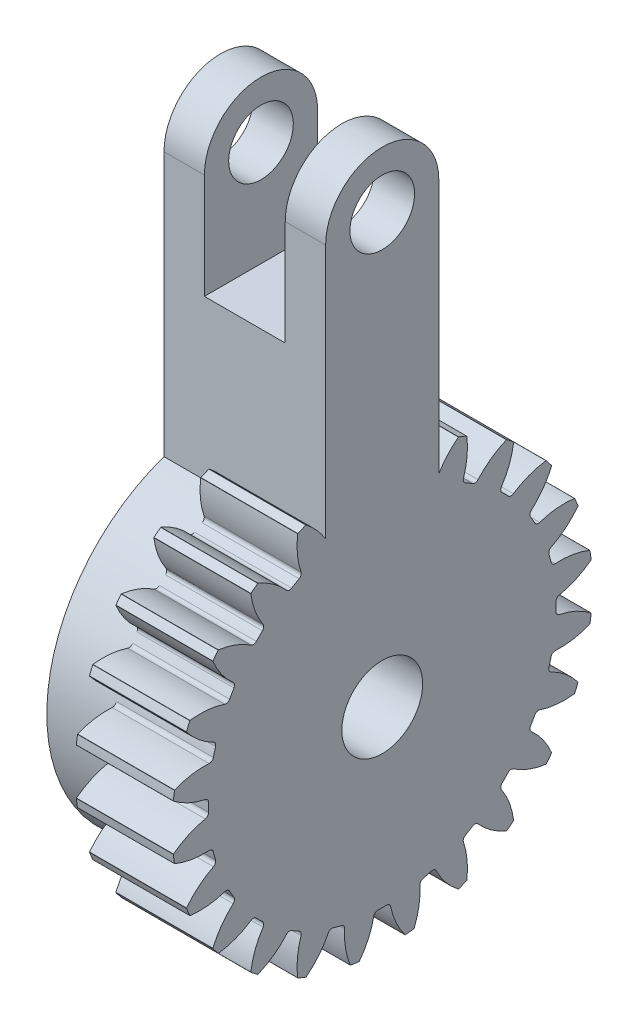
SolidWorks part; units mm, degrees
material "Nylon 101"
ref_plane "Plane1" through (0, 0, 0) normal (0, 0, 1) x (1, 0, 0)
ref_plane "Plane2" through (0, 0, 0) normal (0, 1, 0) x (1, 0, 0)
ref_plane "Plane3" through (0, 0, 0) normal (1, 0, 0) x (0, 0, -1)
sketch "HoldingSke" plane through (0, 0, 0) normal (0, 1, 0) x (1, 0, 0)
  line L0 (0, 0) -> (0.9135, -0.4067)
  line L1 (-15, 0) -> (100, 0) construction
  line L2 (0, 0) -> (-2.1039, 2.3779)
  line L3 (0, 0) -> (-11.863, 4.5341)
  line L4 (0, 0) -> (7.8894, 3.5126)
  line L5 (0, 0) -> (-46.8476, -17.4728)
  line L6 (0, 0) -> (-4.9738, -3.3558)
  line L7 (-2.1039, 2.3779) -> (8.6589, 51.2073)
  line L8 (-76.2, 54.61) -> (-75.5, 54.61)
  line L9 (-71.009, 38.7566) -> (-53.1078, 45.2721)
  line L10 (-76.2, 71.12) -> (104.1128, 71.12)
  line L11 (0, 0) -> (-6, 0)
  line L12 (-76.2, 101.6) -> (-76.162, 101.6)
  line L13 (24.9733, 27.94) -> (52.9518, 28.4284)
  line L14 (24.9733, 27.94) -> (24.9743, 27.94)
  line L15 (24.9733, 27.94) -> (100.4006, 29.5858)
  line L16 (-63.627, -1) -> (-12.827, -1)
  circle A0 centre (0, 0) radius 2
  circle A1 centre (0, 0) radius 10.749
  circle A2 centre (0, 0) radius 37.5
  circle A3 centre (0, 0) radius 2
  dimension "MHD" = 21.498
  dimension "Hub_dia" = 75
  dimension "Bore" = 4
  dimension "MBD" = 4
  dimension "Num_teeth" = 24
  dimension "Pitch" = 1
  dimension "Overall_len" = 50
  dimension "Show_teeth" = 24
  dimension "Thickness" = 6
  dimension "OAL" = 50.0015
  dimension "T_dim" = 0.7
  dimension "Ap" = 20
  dimension "H" = 19.05
  dimension "Pitch_radius" = 180.3128
  dimension "Width" = 6
  dimension "Backlash" = 0.038
  dimension "Addendum_fac" = 1
  dimension "Dedendum_fac" = 1.25
  dimension "Clearance_fac" = 0.25
  dimension "Dedendum_add" = 0.001
  dimension "Module" = 1
sketch "BasProSke" plane through (0, 0, 0) normal (0, 1, 0) x (1, 0, 0)
  line L0 (-10, 0) -> (60, 0) construction
  line L1 (0, 0) -> (0, 13)
  line L2 (0, 0) -> (6, 0)
  line L3 (6, 0) -> (6, 13)
  line L4 (6, 13) -> (0, 13)
  dimension "Thickness" = 6
  dimension "Diameter" = 26
revolve "Base-Revolve" add sketch "BasProSke" angle 360 about L0
sketch "TooCutSke" plane through (0, 0, 0) normal (1, 0, 0) x (0, 0, -1)
  line L1 (0, 0) -> (0, 107) construction
  line L2 (0, 0) -> (-0.8513, 11.9698) construction
  line L3 (0, 0) -> (-3.127, 23.752) construction
  line L4 (-0.8513, 11.9698) -> (-1.5635, 11.876) construction
  arc A0 (0.4834, 10.7381) -> (-0.4834, 10.7381) centre (0, 0) ccw
  arc A1 (1.4409, 12.9455) -> (-1.4409, 12.9455) centre (0, 0) ccw
  circle A2 centre (0, 0) radius 12 construction
  circle A3 centre (0, 0) radius 11.2763 construction
  arc A4 (-0.4834, 10.7381) -> (-1.4409, 12.9455) centre (-5.2252, 9.9926) ccw
  arc A5 (1.4409, 12.9455) -> (0.4834, 10.7381) centre (5.2252, 9.9926) ccw
  dimension "Root_dia" = 21.498
  dimension "Overcut_dia" = 26.0508
  dimension "Pitch_dia" = 24
  dimension "Base_dia" = 22.5526
  dimension "Flank_rad" = 4.8
  dimension "Half_ang" = 7.5
  dimension "Half_CT" = 0.7183
extrude "ToothCut" cut sketch "TooCutSke" along normal through all
fillet "Breaks" radius 0.02 2 edges at (3, 12.9219, -1.4227) (3, 12.9219, 1.4227)
fillet "RootFillets" radius 0.251 2 edges at (3, 10.7381, -0.4834) (3, 10.7381, 0.4834)
pattern_circular "TeethCuts" count 24 over 360 about axis through (0, 0, 0) along (1, 0, 0) of "ToothCut", "RootFillets", "Breaks"
sketch "HubNeaOneSke" plane through (0, 0, 0) normal (-1, 0, 0) x (0, 0, 1)
  circle A0 centre (0, 0) radius 10.749
  dimension "Diameter" = 21.498
extrude "HubNearOne" add sketch "HubNeaOneSke" along normal blind 4
sketch "HubNeaBotSke" plane through (0, 0, 0) normal (-1, 0, 0) x (0, 0, 1)
  circle A0 centre (0, 0) radius 10.749
  dimension "Diameter" = 21.498
extrude "HubNearBoth" add sketch "HubNeaBotSke" along normal blind 4
sketch "BorSke" plane through (0, 0, 0) normal (1, 0, 0) x (0, 0, -1)
  circle A0 centre (0, 0) radius 2.5
  dimension "Diameter" = 5
extrude "Bore" cut sketch "BorSke" along normal mid plane 100.003
ref_plane "FarPln" through (6, 0, 0) normal (1, 0, 0) x (0, 0, -1)
sketch "HubFarSke" plane through (6, 0, 0) normal (1, 0, 0) x (0, 0, -1)
  circle A0 centre (0, 0) radius 10.749
  dimension "Diameter" = 21.498
extrude "HubFar" [suppressed] add sketch "HubFarSke" along normal blind 22.0008
sketch "Эскиз1" plane through (0, 0, 0) normal (-1, 0, 0) x (0, 0, 1)
  circle A0 centre (0, 0) radius 9
  dimension "D1" = 18
extrude "Бобышка-Вытянуть1" add sketch "Эскиз1" along normal blind 4
sketch "Эскиз2" plane through (-4, 0, 0) normal (-1, 0, 0) x (0, 0, 1)
  circle A0 centre (0, 0) radius 2.5
  dimension "D1" = 5
extrude "Вырез-Вытянуть1" cut sketch "Эскиз2" against normal through all
sketch "Эскиз3" plane through (0, 0, 0) normal (1, 0, 0) x (0, 0, -1)
  line L0 (0, 0) -> (0, 30) construction
  line L1 (-3.5, 26.5) -> (-3.5, 7)
  line L2 (3.5, 26.5) -> (3.5, 7)
  line L4 (3.5, 7) -> (-3.5, 7)
  arc A0 (-3.5, 26.5) -> (3.5, 26.5) centre (0, 26.5) cw
  dimension "D4" = 7
  dimension "D3" = 3.5
  dimension "D1" = 30
  dimension "D2" = 26.5
extrude "Бобышка-Вытянуть2" add sketch "Эскиз3" along normal blind 6 and the other way blind 4
sketch "Эскиз4" plane through (0, 0, 0) normal (0, 0, 1) x (1, 0, 0)
  line L0 (-1.5, 32) -> (3.5, 32)
  line L1 (-1.5, 32) -> (-1.5, 20)
  line L2 (-1.5, 20) -> (3.5, 20)
  line L3 (3.5, 32) -> (3.5, 20)
  line L4 (0, 10.749) -> (0, -10.749) construction
  line L5 (-4, 30) -> (-4, 26.5) construction
  point P6 (0, 0)
  dimension "D1" = 12
  dimension "D2" = 5
  dimension "D3" = 20
  dimension "D4" = 2.5
extrude "Вырез-Вытянуть2" cut sketch "Эскиз4" against normal through all both and the other way through all
hole_wizard "Отверстие с зазором M41" positions "Эскиз7" profile "Эскиз6" hole size "M4" standard "JIS"
sketch "Эскиз7" plane through (6, 0, 0) normal (1, 0, 0) x (0, 0, -1)
  line L0 (3.5, 10.74) -> (3.5, 26.5) construction
  arc A1 (3.5, 26.5) -> (-3.5, 26.5) centre (0, 26.5) ccw construction
  point P0 (0, 26.5)
  point P17 (0, 30)
  dimension "D1" = 3.5
  dimension "D2" = 3.5
sketch "Эскиз6" plane through (6, 26.5, 0) normal (0, 1, 0) x (0, 0, -1)
  line L0 (0, 0) -> (0, 16.2017)
  line L1 (0, 16.2017) -> (2, 15)
  line L2 (2, 15) -> (2, 0)
  line L5 (2, 0) -> (0, 0)
  line L10 (0, 16.2017) -> (-2, 15) construction
  line L11 (0, -6.35) -> (0, 107.95) construction
  dimension "Диаметр отверстия" = 4
  dimension "Глубина отверстия" = 15
  dimension "Угол заточки сверла" = 118
equation "' \"Module@HoldingSke\" = 6.35"
equation "' \"Num_teeth@HoldingSke\" = 12"
equation "' \"Ap@HoldingSke\" =  20"
equation "' \"Ap@HoldingSke\" = 20"
equation "' \"Width@HoldingSke\" = 0.5 * 25.4"
equation "' \"Hub_dia@HoldingSke\"= 1 * 25.4"
equation "' \"Hub_dia@HoldingSke\" = 1 * 25.4"
equation "' \"Overall_len@HoldingSke\" = 1.0 * 25.4"
equation "' \"Bore@HoldingSke\" = 0.75 * 25.4"
equation "' \"T_dim@HoldingSke\" = 0.1 * 25.4"
equation "' \"Width@KeySke\" = 0.25 * 25.4"
equation "' \"Show_teeth@HoldingSke\" = 13"
equation "' \"Backlash@HoldingSke\" = 0.009 * 25.4"
equation "' \"Addendum_fac@HoldingSke\" = 1.0"
equation "' \"Dedendum_fac@HoldingSke\" = 1.25"
equation "' \"Dedendum_add@HoldingSke\" = 0.00005 * 25.4"
equation "' \"Clearance_fac@HoldingSke\" = 0.25"
equation "\"Pitch@HoldingSke\" = 1 / \"Module@HoldingSke\""
equation "\"Overcut_dia@TooCutSke\" = (\"Num_teeth@HoldingSke\" + 2 * \"Addendum_fac@HoldingSke\") / \"Pitch@HoldingSke\" + 0.002 * 25.4"
equation "\"Pitch_dia@TooCutSke\" = \"Num_teeth@HoldingSke\" / \"Pitch@HoldingSke\""
equation "\"Base_dia@TooCutSke\" = \"Num_teeth@HoldingSke\" / \"Pitch@HoldingSke\" * cos((\"Ap@HoldingSke\"  * 3.14159265 / 180))"
equation "\"Root_dia@TooCutSke\" = (\"Num_teeth@HoldingSke\" + 2) / \"Pitch@HoldingSke\" - 2 * (\"Addendum_fac@HoldingSke\" + \"Dedendum_fac@HoldingSke\") / \"Pitch@HoldingSke\" - \"Dedendum_add@HoldingSke\" * 2"
equation "\"Half_ang@TooCutSke\" = 180 / \"Num_teeth@HoldingSke\""
equation "\"Half_CT@TooCutSke\" = \"Num_teeth@HoldingSke\" / \"Pitch@HoldingSke\" * sin((3.14159265 / 2 / \"Num_teeth@HoldingSke\")) / 2 - 7 * \"Backlash@HoldingSke\" / 4"
equation "\"Flank_rad@TooCutSke\" = \"Num_teeth@HoldingSke\" / \"Pitch@HoldingSke\" / 5"
equation "\"Radius@RootFillets\" = \"Clearance_fac@HoldingSke\" / \"Pitch@HoldingSke\" + \"Dedendum_add@HoldingSke\""
equation "\"Break_rad@Breaks\" = 0.02 / \"Pitch@HoldingSke\""
equation "\"Thickness@HoldingSke\" = \"Width@HoldingSke\""
equation "\"OAL@HoldingSke\" = \"Thickness@HoldingSke\""
equation "\"MHD@HoldingSke\" = (\"Num_teeth@HoldingSke\" + 2) / \"Pitch@HoldingSke\" - 2 * (\"Addendum_fac@HoldingSke\" + \"Dedendum_fac@HoldingSke\")  / \"Pitch@HoldingSke\" - \"Dedendum_add@HoldingSke\" * 2"
equation "\"MBD@HoldingSke\" = (\"Num_teeth@HoldingSke\" + 2) / \"Pitch@HoldingSke\" - 2 * (\"Addendum_fac@HoldingSke\" + \"Dedendum_fac@HoldingSke\")  / \"Pitch@HoldingSke\" - \"Dedendum_add@HoldingSke\" * 2 - 0.002 * 25.4"
equation "\"MHD@HoldingSke\" = ((sgn( \"MHD@HoldingSke\" - \"Hub_dia@HoldingSke\" )-1)*( \"MHD@HoldingSke\" - \"Hub_dia@HoldingSke\" ))/-2+ \"Hub_dia@HoldingSke\""
equation "\"MBD@HoldingSke\" = ((sgn( \"MBD@HoldingSke\" - \"Bore@HoldingSke\" )-1)*( \"MBD@HoldingSke\" - \"Bore@HoldingSke\" ))/-2+ \"Bore@HoldingSke\""
equation "\"OAL@HoldingSke\" = ((sgn( \"OAL@HoldingSke\" - \"Overall_len@HoldingSke\" )+1)*( \"OAL@HoldingSke\" - \"Overall_len@HoldingSke\" ))/2 + \"Overall_len@HoldingSke\" + 0.000002 * 25.4"
equation "\"Num_teeth@TeethCuts\" = int( \"Show_teeth@HoldingSke\" ) + 1"
equation "\"Num_teeth@TeethCuts\" = ((sgn( \"Num_teeth@TeethCuts\" - \"Num_teeth@HoldingSke\" )-1)*( \"Num_teeth@TeethCuts\" - \"Num_teeth@HoldingSke\" ))/-2+ \"Num_teeth@HoldingSke\""
equation "\"Num_teeth@TeethCuts\" = ((sgn( \"Num_teeth@TeethCuts\" - 2.0)+1)*( \"Num_teeth@TeethCuts\" - 2.0))/2 +2.0"
equation "\"Angle@TeethCuts\" = 360.0 / \"Num_teeth@HoldingSke\""
equation "\"Diameter@BasProSke\" = (\"Num_teeth@HoldingSke\" + 2 * \"Addendum_fac@HoldingSke\") / \"Pitch@HoldingSke\""
equation "\"Thickness@BasProSke\"  = \"Thickness@HoldingSke\""
equation "' \"Fillet_rad@BasProSke\" =  \"Thickness@HoldingSke\" * 0.05"
equation "' \"Fillet_rad@BasProSke\" = \"Thickness@HoldingSke\" * 0.05"
equation "\"MHD@HoldingSke\" = ((sgn( \"MHD@HoldingSke\" - \"Root_dia@TooCutSke\" )-1)*( \"MHD@HoldingSke\" - \"Root_dia@TooCutSke\" ))/-2+ \"Root_dia@TooCutSke\""
equation "\"Diameter@HubNeaOneSke\" = \"MHD@HoldingSke\""
equation "\"Diameter@HubNeaBotSke\" = \"MHD@HoldingSke\""
equation "\"Thickness@FarPln\" = \"Thickness@BasProSke\""
equation "\"Diameter@HubFarSke\" = \"MHD@HoldingSke\""
equation "\"Length@HubFar\" = ( \"OAL@HoldingSke\" - \"Thickness@BasProSke\" ) / 2.0"
equation "\"D1@Bore\" = \"OAL@HoldingSke\" * 2.0"
